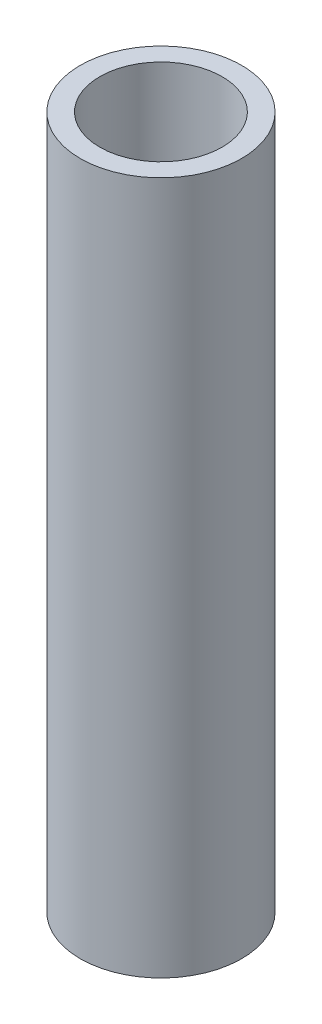
SolidWorks part; units mm, degrees
material "PVC 0.007 Plasticized"
ref_plane "Front Plane" through (0, 0, 0) normal (0, 0, 1) x (1, 0, 0)
ref_plane "Top Plane" through (0, 0, 0) normal (0, 1, 0) x (1, 0, 0)
ref_plane "Right Plane" through (0, 0, 0) normal (1, 0, 0) x (0, 0, -1)
sketch "Sketch1" plane through (0, 0, 0) normal (0, 1, 0) x (1, 0, 0)
  circle A0 centre (0, 0) radius 12.573
  circle A1 centre (0, 0) radius 9.525
  dimension "D1" = 19.05
  dimension "D2" = 25.146
extrude "Boss-Extrude1" add sketch "Sketch1" along normal blind 107.95
